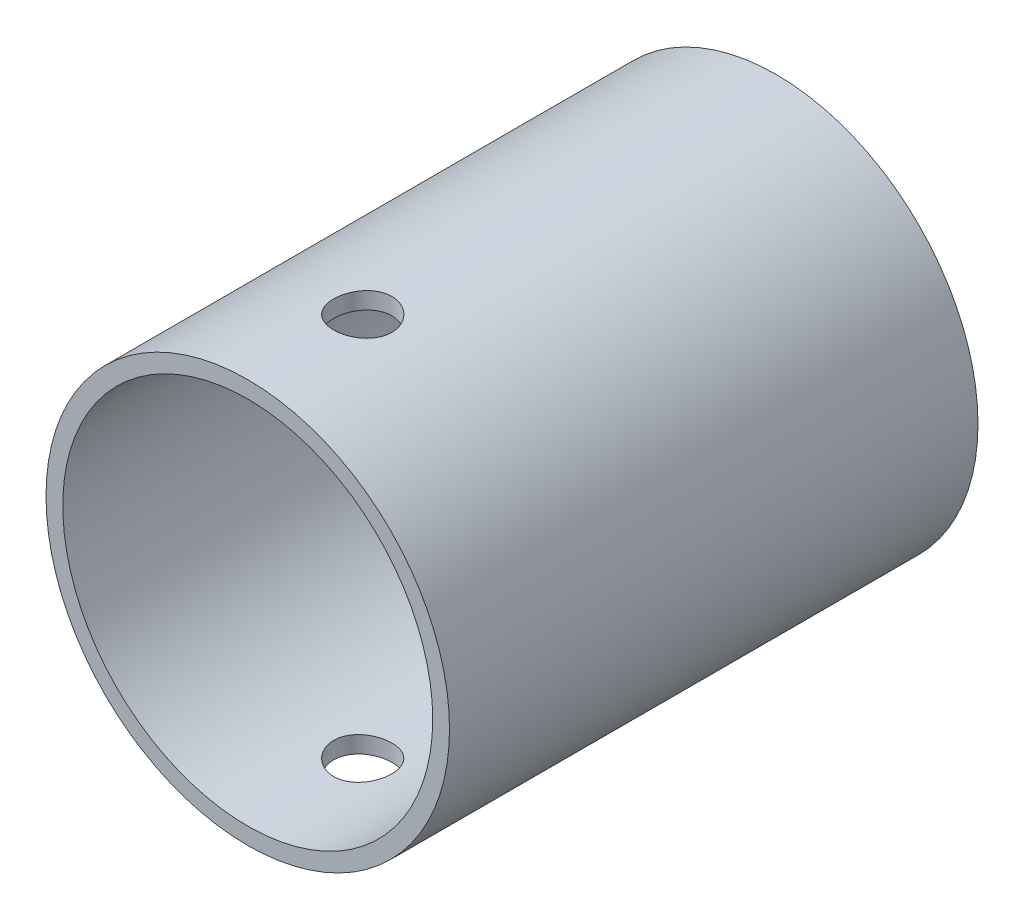
SolidWorks part; units mm, degrees
material "Hexcel AS4C (3000 Filaments)"
ref_plane "Front Plane" through (0, 0, 0) normal (0, 0, 1) x (1, 0, 0)
ref_plane "Top Plane" through (0, 0, 0) normal (0, 1, 0) x (1, 0, 0)
ref_plane "Right Plane" through (0, 0, 0) normal (1, 0, 0) x (0, 0, -1)
sketch "Sketch1" plane through (0, 0, 0) normal (0, 0, 1) x (1, 0, 0)
  circle A0 centre (0, 0) radius 17.5
  circle A1 centre (0, 0) radius 19.0875
  dimension "D1" = 35
  dimension "D2" = 38.175
extrude "Boss-Extrude1" add sketch "Sketch1" along normal blind 50
sketch "Sketch2" plane through (0, 0, 0) normal (0, 0, -1) x (-1, 0, 0)
  circle A0 centre (0, 0) radius 17.5
  circle A1 centre (0, 0) radius 6
  dimension "D1" = 35
  dimension "D2" = 12
extrude "Boss-Extrude2" add sketch "Sketch2" against normal blind 5
sketch "Sketch3" plane through (0, 0, 5) normal (0, 0, 1) x (1, 0, 0)
  circle A0 centre (0, 0) radius 17.5
  circle A1 centre (0, 0) radius 9
  dimension "D1" = 35
  dimension "D2" = 18
extrude "Boss-Extrude3" add sketch "Sketch3" along normal blind 1
sketch "Sketch4" plane through (0, 0, 6) normal (0, 0, 1) x (1, 0, 0)
  circle A0 centre (0, 0) radius 17.5
  circle A1 centre (0, 0) radius 10
  dimension "D1" = 35
  dimension "D2" = 20
extrude "Boss-Extrude4" add sketch "Sketch4" along normal blind 12
sketch "Sketch5" plane through (0, 0, 0) normal (0, 1, 0) x (1, 0, 0)
  line L0 (0, -50) -> (0, -39.12) construction
  line L1 (-17.5, -50) -> (17.5, -50) construction
hole_wizard "M5 Clearance Hole1" positions "Sketch6" profile "Sketch7" hole size "M5" standard "ANSI Metric"
sketch "Sketch6" plane through (0, 0, 0) normal (0, 1, 0) x (1, 0, 0)
  point P0 (0, -39.12)
sketch "Sketch7" plane through (0, 0, 39.12) normal (1, 0, 0) x (0, 0, -1)
  line L0 (0, 0) -> (0, 19.0875)
  line L1 (0, 19.0875) -> (2.75, 19.0875)
  line L2 (2.75, 19.0875) -> (2.75, 0)
  line L5 (2.75, 0) -> (0, 0)
  line L11 (0, -6.35) -> (0, 107.95) construction
  dimension "Thru Hole Dia." = 5.5
  dimension "Thru Hole Depth" = 19.0875
mirror "Mirror1" about plane through (0, 0, 0) normal (0, 1, 0) of "M5 Clearance Hole1"
equation "\"tubeOutDiameter\" = 35mm"
equation "\"wheelShaftDiameter\"= 12mm"
equation "\"wheelThickness\"= 135mm"
equation "\"D2@Sketch1\"=\"tubeOutDiameter\"+0.125in"
equation "\"D1@Sketch2\"=\"tubeOutDiameter\""
equation "\"D1@Sketch3\"=\"tubeOutDiameter\""
equation "\"BearingDiameter\"= 20mm"
equation "\"D1@Sketch4\"=\"tubeOutDiameter\""
equation "\"D2@Sketch4\"=\"BearingDiameter\""
equation "\"BearingThickness\"= 10mm"
equation "\"D1@Boss-Extrude4\"=\"BearingThickness\"+2mm"
equation "\"D2@Sketch3\"=\"BearingDiameter\"-2mm"
